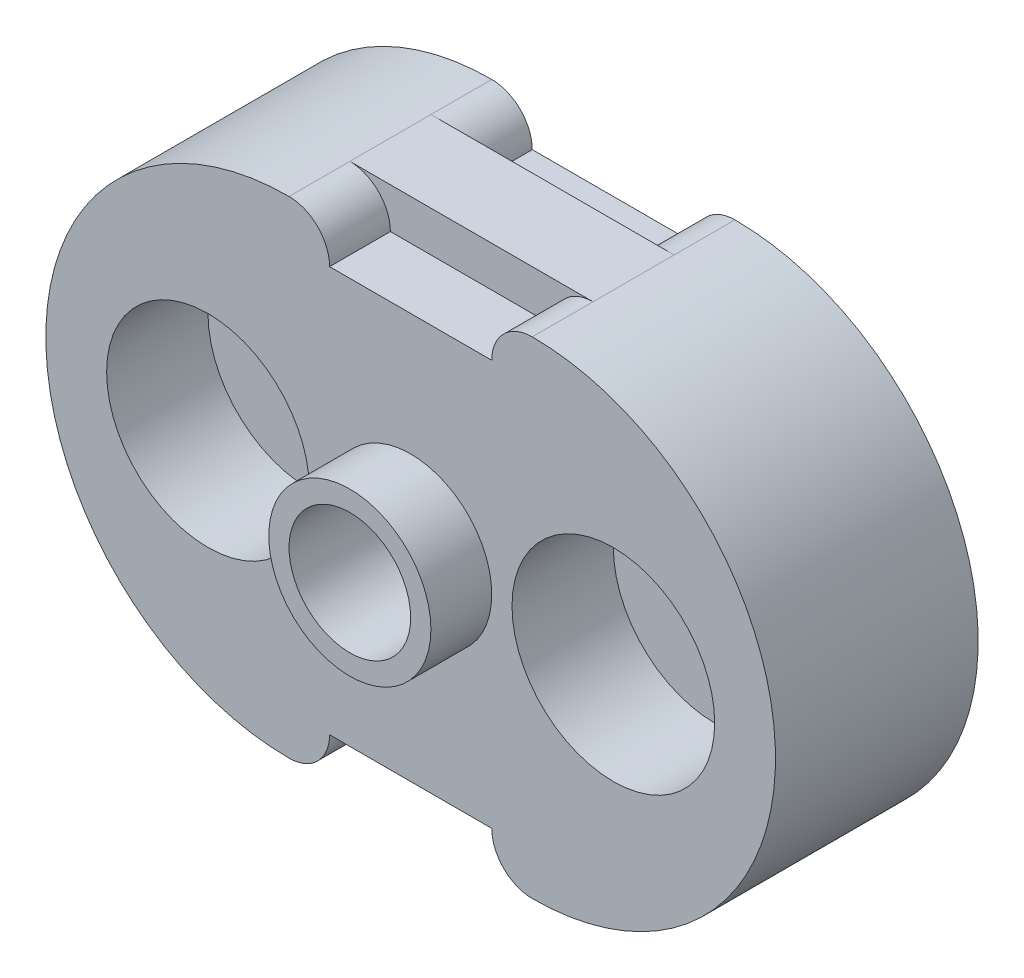
SolidWorks part; units mm, degrees
ref_plane "Front Plane" through (0, 0, 0) normal (0, 0, 1) x (1, 0, 0)
ref_plane "Top Plane" through (0, 0, 0) normal (0, 1, 0) x (1, 0, 0)
ref_plane "Right Plane" through (0, 0, 0) normal (1, 0, 0) x (0, 0, -1)
sketch "Sketch1" plane through (0, 0, 0) normal (0, 0, 1) x (1, 0, 0)
  line L0 (-30, 30) -> (0, 30) construction
  line L1 (-30, 60) -> (0, 60)
  line L2 (-30, 0) -> (0, 0)
  arc A0 (-30, 60) -> (-30, 0) centre (-30, 30) ccw
  arc A1 (0, 0) -> (0, 60) centre (0, 30) ccw
  point P2 (-15, 30)
  dimension "D2" = 30
  dimension "D1" = 30
extrude "Boss-Extrude1" add sketch "Sketch1" along normal blind 10
sketch "Sketch2" plane through (0, 0, 10) normal (0, 0, 1) x (1, 0, 0)
  line L0 (-25, 55) -> (-5, 55)
  line L1 (0, 60) -> (-30, 60) construction
  line L2 (-25, 5) -> (-5, 5)
  line L3 (-30, 0) -> (0, 0) construction
  arc A0 (-5, 55) -> (0, 60) centre (0, 55) cw
  arc A1 (-25, 55) -> (-30, 60) centre (-30, 55) ccw
  arc A2 (-5, 5) -> (0, 0) centre (0, 5) ccw
  arc A3 (-25, 5) -> (-30, 0) centre (-30, 5) cw
  arc A4 (0, 60) -> (0, 0) centre (0, 30) cw
  arc A5 (-30, 60) -> (-30, 0) centre (-30, 30) ccw
  dimension "D1" = 5
  dimension "D2" = 5
  dimension "D7" = 5
  dimension "D3" = 5
  dimension "D4" = 20
  dimension "D5" = 5
  dimension "D6" = 5
  dimension "D8" = 5
extrude "Boss-Extrude2" add sketch "Sketch2" along normal blind 7.5
sketch "Sketch3" plane through (0, 0, 0) normal (0, 0, -1) x (-1, 0, 0)
  line L0 (5, 55) -> (25, 55)
  line L1 (0, 60) -> (30, 60) construction
  line L2 (5, 5) -> (25, 5)
  line L3 (30, 0) -> (0, 0) construction
  arc A0 (25, 5) -> (30, 0) centre (30, 5) ccw
  arc A1 (5, 5) -> (0, 0) centre (0, 5) cw
  arc A2 (25, 55) -> (30, 60) centre (30, 55) cw
  arc A3 (5, 55) -> (0, 60) centre (0, 55) ccw
  arc A4 (30, 0) -> (30, 60) centre (30, 30) ccw
  arc A5 (0, 60) -> (0, 0) centre (0, 30) ccw
  dimension "D7" = 5
  dimension "D9" = 5
  dimension "D1" = 20
  dimension "D2" = 5
  dimension "D3" = 5
  dimension "D4" = 20
  dimension "D5" = 5
  dimension "D6" = 5
  dimension "D8" = 5
extrude "Boss-Extrude3" add sketch "Sketch3" along normal blind 7.5
sketch "Sketch4" plane through (0, 0, -7.5) normal (0, 0, -1) x (-1, 0, 0)
  line L0 (-5, 30) -> (35, 30) construction
  line L1 (-5, 50) -> (35, 50)
  line L2 (-5, 10) -> (35, 10)
  line L3 (25, 55) -> (5, 55) construction
  line L5 (5, 5) -> (25, 5) construction
  arc A0 (-5, 50) -> (-5, 10) centre (-5, 30) ccw
  arc A1 (35, 10) -> (35, 50) centre (35, 30) ccw
  point P3 (15, 30)
  dimension "D3" = 5
  dimension "D1" = 5
  dimension "D2" = 5
  dimension "D4" = 5
extrude "Cut-Extrude1" cut sketch "Sketch4" against normal blind 7.5
sketch "Sketch5" plane through (0, 0, 17.5) normal (0, 0, 1) x (1, 0, 0)
  circle A0 centre (10, 30) radius 12.5
  circle A1 centre (-40, 30) radius 12.5
  dimension "D1" = 25
  dimension "D4" = 30
  dimension "D2" = 10
  dimension "D3" = 30
  dimension "D5" = 10
extrude "Cut-Extrude3" cut sketch "Sketch5" against normal blind 12.5
sketch "Sketch6" plane through (0, 0, 5) normal (0, 0, 1) x (1, 0, 0)
  circle A0 centre (10, 30) radius 5
  circle A1 centre (-40, 30) radius 5
  point P0 (-40, 30)
  point P1 (10, 30)
  dimension "D1" = 10
  dimension "D2" = 10
extrude "Cut-Extrude4" cut sketch "Sketch6" against normal blind 17.5
sketch "Sketch7" plane through (0, 0, 17.5) normal (0, 0, 1) x (1, 0, 0)
  circle A0 centre (-15, 30) radius 10
  circle A1 centre (10, 30) radius 12.5 construction
  point P2 (10, 30)
  dimension "D1" = 20
  dimension "D2" = 25
extrude "Boss-Extrude4" add sketch "Sketch7" along normal blind 7.5
sketch "Sketch8" plane through (0, 0, 25) normal (0, 0, 1) x (1, 0, 0)
  circle A0 centre (-15, 30) radius 7.5
  dimension "D1" = 15
extrude "Cut-Extrude5" cut sketch "Sketch8" against normal blind 25
sketch "Sketch10" plane through (0, 0, 0) normal (0, 0, -1) x (-1, 0, 0)
  circle A0 centre (15, 30) radius 15
  point P0 (15, 30)
  dimension "D1" = 30
extrude "Boss-Extrude6" add sketch "Sketch10" along normal blind 15
sketch "Sketch11" plane through (0, 0, -15) normal (0, 0, -1) x (-1, 0, 0)
  circle A0 centre (15, 30) radius 7.5
  dimension "D1" = 15
extrude "Cut-Extrude6" cut sketch "Sketch11" against normal blind 20
